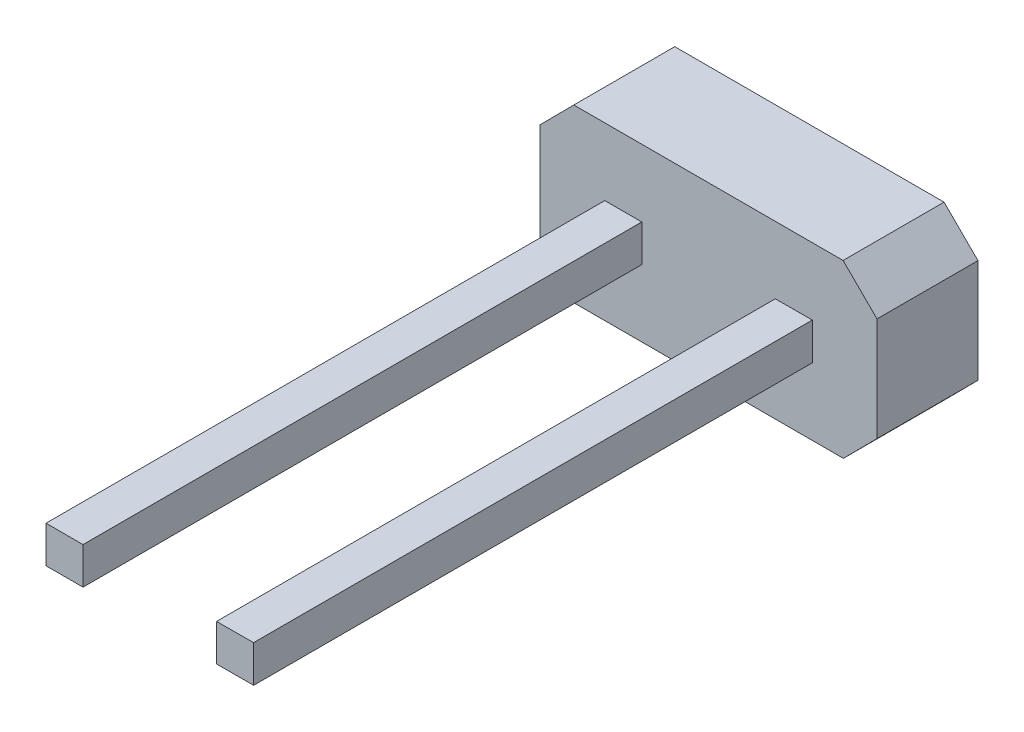
SolidWorks part; units mm, degrees
ref_plane "Front Plane" through (0, 0, 0) normal (0, 0, 1) x (1, 0, 0)
ref_plane "Top Plane" through (0, 0, 0) normal (0, 1, 0) x (1, 0, 0)
ref_plane "Right Plane" through (0, 0, 0) normal (1, 0, 0) x (0, 0, -1)
sketch "Sketch1" plane through (0, 0, 0) normal (0, 0, 1) x (1, 0, 0)
  line L0 (-1.9296, 0) -> (2.0704, 0)
  line L1 (2.0704, 0) -> (2.5704, 0.5041)
  line L2 (2.5704, 0.5041) -> (2.5704, 2.0441)
  line L3 (2.5704, 2.0441) -> (2.0663, 2.5441)
  line L4 (2.0663, 2.5441) -> (-1.9337, 2.5441)
  line L5 (-1.9337, 2.5441) -> (-2.4337, 2.04)
  line L6 (-2.4337, 2.04) -> (-2.4337, 0.5)
  line L7 (-2.4337, 0.5) -> (-1.9296, 0)
  dimension "D1" = 4
  dimension "D2" = 4
  dimension "D3" = 1.54
  dimension "D4" = 1.54
  dimension "D5" = 0.71
  dimension "D6" = 0.71
  dimension "D7" = 0.71
  dimension "D8" = 0.71
  dimension "D9" = 0.5
extrude "Boss-Extrude1" add sketch "Sketch1" along normal blind 1.5
sketch "Sketch2" plane through (0, 0, 1.5) normal (0, 0, 1) x (1, 0, 0)
  line L0 (-2.4337, 2.04) -> (-2.4337, 0.5) construction
  line L1 (-1.4737, 1.5441) -> (-0.9237, 1.5441)
  line L2 (-1.4737, 1.5441) -> (-1.4737, 0.9959)
  line L3 (-1.4737, 0.9959) -> (-0.9237, 0.9959)
  line L4 (-0.9237, 1.5441) -> (-0.9237, 0.9959)
  line L5 (2.0663, 2.5441) -> (-1.9337, 2.5441) construction
  line L6 (-1.9296, 0) -> (2.0704, 0) construction
  line L7 (0.0663, 2.5441) -> (0.0704, 0) construction
  line L8 (1.6112, 1.0009) -> (1.0612, 0.9991)
  line L9 (1.0595, 1.5473) -> (1.0612, 0.9991)
  line L10 (1.6095, 1.549) -> (1.0595, 1.5473)
  line L11 (1.6095, 1.549) -> (1.6112, 1.0009)
  point P4 (-1.4737, 1.27)
  point P7 (-2.4337, 1.27)
  dimension "D1" = 0.96
  dimension "D2" = 1
  dimension "D3" = 0.55
extrude "Boss-Extrude2" add sketch "Sketch2" along normal blind 8.3
